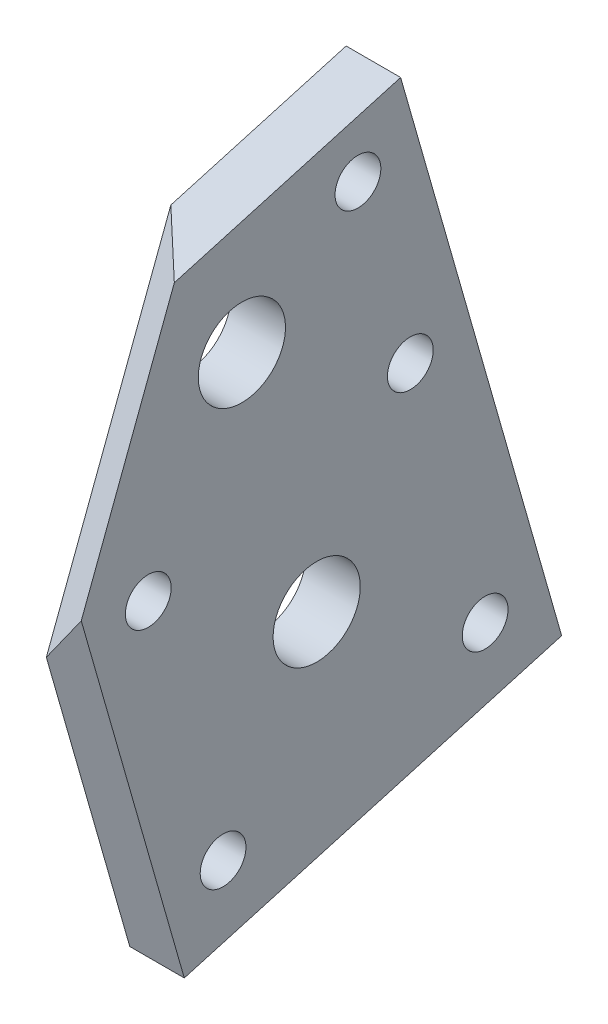
SolidWorks part; units mm, degrees
ref_plane "Front Plane" through (0, 0, 0) normal (0, 0, 1) x (1, 0, 0)
ref_plane "Top Plane" through (0, 0, 0) normal (0, 1, 0) x (1, 0, 0)
ref_plane "Right Plane" through (0, 0, 0) normal (1, 0, 0) x (0, 0, -1)
sketch "Sketch2" plane through (0, 629.4399, -2204.4624) normal (0, -0.2746, 0.9616) x (1, 0, 0)
  line L1 (-196.8236, 2516.2401) -> (-191.8236, 2516.2401)
  line L2 (-196.8236, 2516.2401) -> (-196.8236, 2570.0401)
  line L3 (-196.8236, 2570.0401) -> (-191.8236, 2570.0401)
  line L4 (-191.8236, 2516.2401) -> (-191.8236, 2570.0401)
  line L10 (-191.8236, 2516.2401) -> (-181.8236, 2516.2401) construction
  line L11 (-181.8236, 2570.0401) -> (-191.8236, 2570.0401) construction
  dimension "D1" = 5
extrude "Boss-Extrude1" add sketch "Sketch2" along normal up to surface (36 mm away)
sketch "Sketch3" plane through (67.3339, -30.4654, -80.6191) normal (0.6157, -0.2786, -0.7371) x (0.4911, 0.8672, 0.0824)
  line L5 (2395.1458, -2402.3214) -> (2500.7258, -2486.4513)
  line L9 (2395.1458, -2402.3214) -> (2553.0784, -2204.1216)
  line L10 (2500.7258, -2486.4513) -> (2658.6585, -2288.2516)
  line L11 (2553.0784, -2204.1216) -> (2658.6585, -2288.2516)
  line L12 (2597.5832, -2364.8988) -> (2591.6051, -2372.4012) construction
  line L13 (2553.0784, -2204.1216) -> (2748.2842, -2359.6686) construction
extrude "Cut-Extrude1" cut sketch "Sketch3" against normal through all
sketch "Sketch4" plane through (-196.8236, 0, 0) normal (-1, 0, 0) x (0, 0, 1)
  circle A0 centre (-1506.5923, 3053.5307) radius 2.1
  circle A1 centre (-1482.553, 3046.6667) radius 2.1
  circle A2 centre (-1499.7284, 3077.5699) radius 2.1
  circle A3 centre (-1475.6891, 3070.706) radius 2.1
  circle A4 centre (-1470.8844, 3087.5335) radius 2.1
  circle A5 centre (-1494.9236, 3094.3974) radius 2.1
  circle A6 centre (-1484.2768, 3086.1576) radius 4
  circle A7 centre (-1491.1407, 3062.1183) radius 4
  circle A8 centre (-1482.553, 3046.6667) radius 2.1 construction
  circle A9 centre (-1506.5923, 3053.5307) radius 2.1 construction
  circle A10 centre (-1475.6891, 3070.706) radius 2.1 construction
  circle A11 centre (-1491.1407, 3062.1183) radius 4 construction
  circle A12 centre (-1470.8844, 3087.5335) radius 2.1 construction
  circle A13 centre (-1499.7284, 3077.5699) radius 2.1 construction
  circle A14 centre (-1494.9236, 3094.3974) radius 2.1 construction
  circle A15 centre (-1484.2768, 3086.1576) radius 4 construction
extrude "Cut-Extrude2" cut sketch "Sketch4" against normal through all
